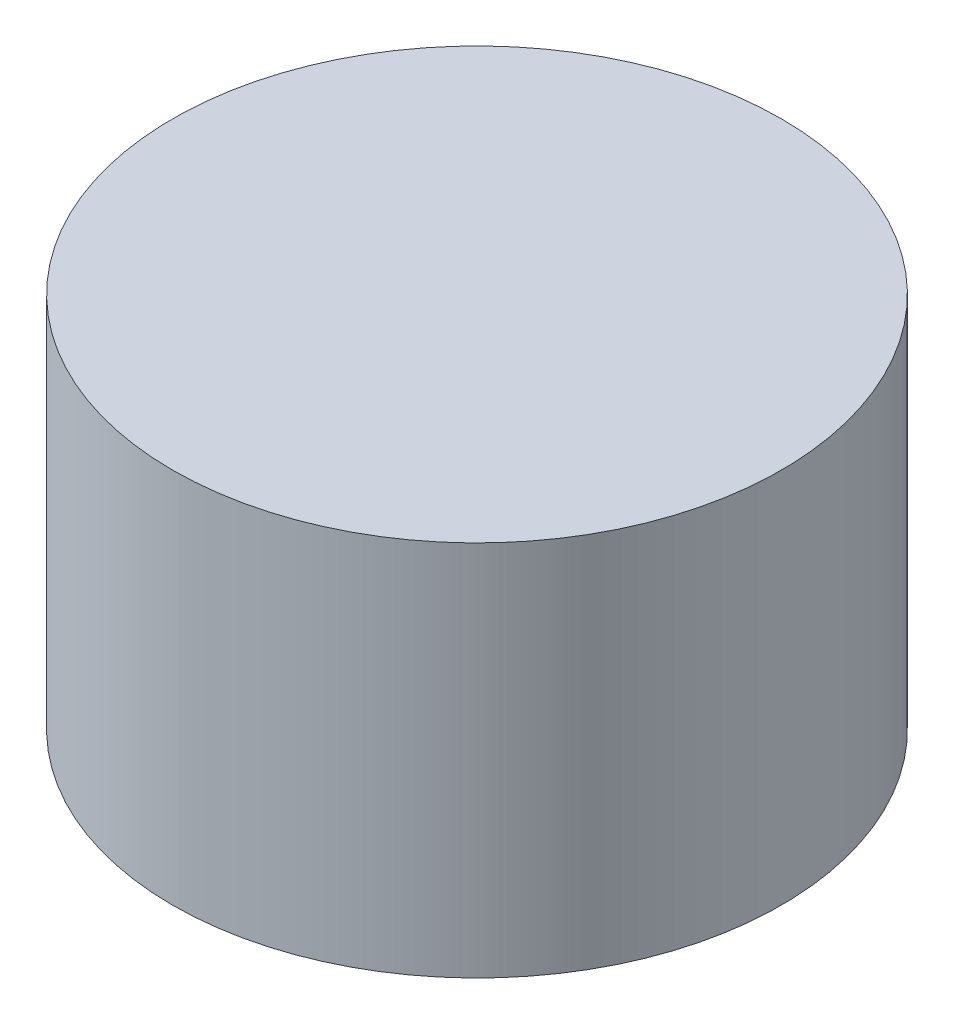
SolidWorks part; units mm, degrees
ref_plane "Front Plane" through (0, 0, 0) normal (0, 0, 1) x (1, 0, 0)
ref_plane "Top Plane" through (0, 0, 0) normal (0, 1, 0) x (1, 0, 0)
ref_plane "Right Plane" through (0, 0, 0) normal (1, 0, 0) x (0, 0, -1)
sketch "Sketch1" plane through (0, 0, 0) normal (0, 1, 0) x (1, 0, 0)
  circle A0 centre (0, 0) radius 10.5
extrude "Boss-Extrude1" add sketch "Sketch1" along normal blind 13
sketch "Sketch2" plane through (0, 0, 0) normal (1, 0, 0) x (0, 0, -1)
  line L0 (0, 8.1741) -> (7.5, 8.1741)
  line L1 (7.5, -1.8259) -> (7.5, 8.1741)
  line L3 (0, 8.1741) -> (0, -1.8259)
  line L4 (-3.4624, -1.8259) -> (-16.0416, -1.8259) construction
  line L5 (7.5, -1.8259) -> (0, -1.8259)
  dimension "D1" = 7.5
  dimension "D2" = 8.1741
  dimension "D3" = 10
sketch "Sketch3" plane through (0, 0, 0) normal (0, 0, 1) x (1, 0, 0)
  line L0 (0, 0.0491) -> (0, 9.5041) construction
revolve "Cut-Revolve2" cut sketch "Sketch2" angle 360 about L0
equation "\"radius\"= 7.5 / 1000"
equation "\"D1@Sketch1\"=\"radius\"*2+.006"
equation "\"a\"= - 32.3127"
equation "\"b\"= .15"
equation "\"c\"=0.005"
equation "\"D1@Boss-Extrude1\"=13/1000"
equation "\"D2@Sketch2\"=\"depth\""
equation "\"critical\"= - \"b\" / 2 / \"a\""
equation "\"critical_height\"= \"c\" + \"b\" * \"critical\" + \"a\" * \"critical\" ^ 2"
equation "\"center_height\"= \"c\""
equation "\"left_height\"= \"c\" + \"b\" * \"radius\" + \"a\" * \"radius\" ^ 2"
equation "\"max_height\"= \"critical_height\""
equation "\"min_height\"= \"center_height\""
equation "\"depth\"= 0.003 + \"c\" + \"max_height\" - \"min_height\""
